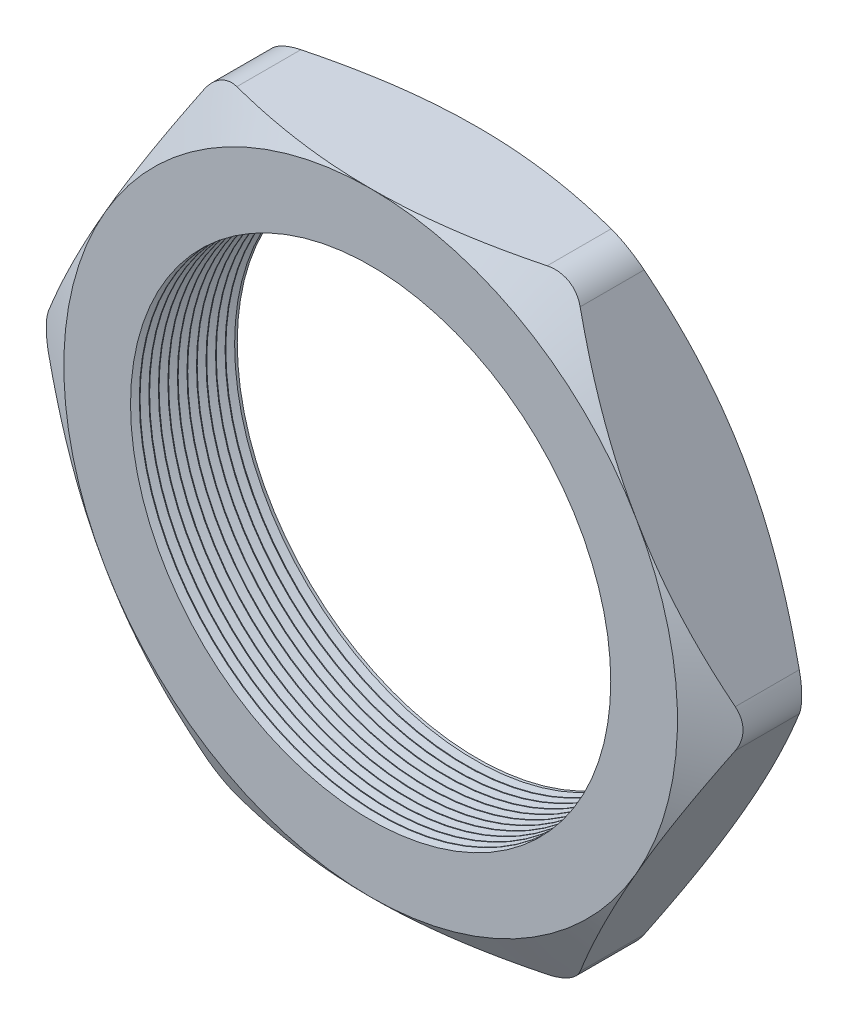
SolidWorks part; units mm, degrees
ref_plane "Front Plane" through (0, 0, 0) normal (0, 0, 1) x (1, 0, 0)
ref_plane "Top Plane" through (0, 0, 0) normal (0, 1, 0) x (1, 0, 0)
ref_plane "Right Plane" through (0, 0, 0) normal (1, 0, 0) x (0, 0, -1)
sketch "Sketch1" plane through (0, 0, 0) normal (0, 0, 1) x (1, 0, 0)
  line L1 (-23.6102, 0) -> (-11.8051, -20.447)
  line L2 (-11.8051, -20.447) -> (11.8051, -20.447)
  line L3 (11.8051, -20.447) -> (23.6102, 0)
  line L4 (23.6102, 0) -> (11.8051, 20.447)
  line L5 (11.8051, 20.447) -> (-11.8051, 20.447)
  line L6 (-11.8051, 20.447) -> (-23.6102, 0)
  circle A0 centre (0, 0) radius 20.447 construction
  circle A1 centre (0, 0) radius 16.002
  dimension "TS" = 32.004
  dimension "H" = 40.894
extrude "Extrude1" add sketch "Sketch1" along normal blind 7.112
sketch "Sketch2" plane through (0, 0, 7.112) normal (0, 0, 1) x (1, 0, 0)
  line L0 (11.8051, 20.447) -> (-11.8051, 20.447) construction
  circle A0 centre (0, 0) radius 20.447
extrude "Cut-Extrude1" cut sketch "Sketch2" against normal through all draft 60 flip side to cut
sketch "Sketch3" plane through (0, 0, 0) normal (0, 0, -1) x (-1, 0, 0)
  line L0 (-11.8051, 20.447) -> (11.8051, 20.447) construction
  circle A0 centre (0, 0) radius 20.447
extrude "Cut-Extrude2" cut sketch "Sketch3" against normal through all draft 60 flip side to cut
fillet "Fillet1" radius 2.54 6 edges at (23.6102, 0, 3.556) (11.8051, -20.447, 3.556) (-11.8051, -20.447, 3.556) (-23.6102, 0, 3.556) (-11.8051, 20.447, 3.556) (11.8051, 20.447, 3.556)
sketch "Sketch4" plane through (0, 0, 0) normal (0, 1, 0) x (1, 0, 0)
  line L0 (-16.002, -7.112) -> (-16.002, -6.5254)
  line L1 (-16.002, 0) -> (-16.002, -7.112) construction
  line L2 (-16.002, -6.5254) -> (-16.51, -6.8187)
  line L3 (-16.51, -6.8187) -> (-16.002, -7.112)
  dimension "D1" = 60
  dimension "D2" = 60
  dimension "D3" = 0.508
revolve "Cut-Revolve1" cut sketch "Sketch4" angle 360 about axis through (0, 0, 0) along (0, 0, 1)
pattern_linear "LPattern1" count 11 spacing 0.635 along (0, 0, -1) of "Cut-Revolve1"
